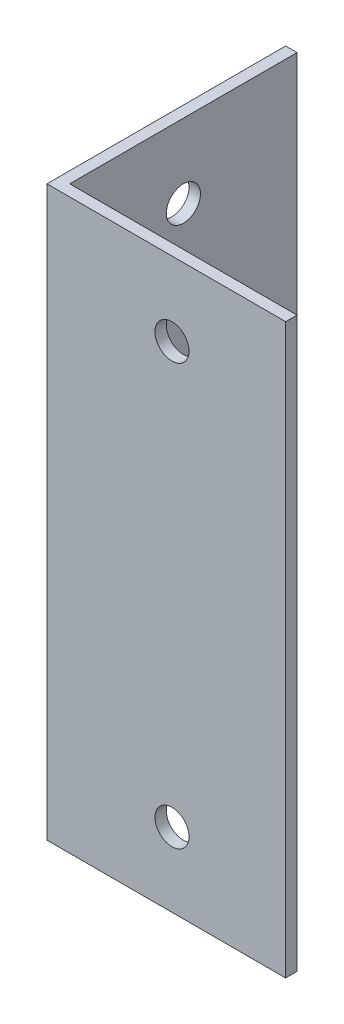
SolidWorks part; units mm, degrees
ref_plane "Face" through (0, 0, 0) normal (0, 0, 1) x (1, 0, 0)
ref_plane "Dessus" through (0, 0, 0) normal (0, 1, 0) x (1, 0, 0)
ref_plane "Droite" through (0, 0, 0) normal (1, 0, 0) x (0, 0, -1)
sketch "Esquisse1" plane through (0, 0, 0) normal (0, 1, 0) x (1, 0, 0)
  line L0 (0, 0) -> (0, 21)
  line L1 (0, 21) -> (1, 21)
  line L2 (1, 21) -> (1, 1)
  line L3 (1, 1) -> (21, 1)
  line L4 (21, 1) -> (21, 0)
  line L5 (21, 0) -> (0, 0)
  dimension "D1" = 1
  dimension "D2" = 1
  dimension "D3" = 90
  dimension "D4" = 20
extrude "Extrusion1" add sketch "Esquisse1" along normal blind 50
sketch "Esquisse2" plane through (1, 0, 0) normal (1, 0, 0) x (0, 0, -1)
  line L0 (1, 25) -> (21, 25) construction
  line L1 (1, 50) -> (1, 0) construction
  line L2 (21, 50) -> (21, 0) construction
  line L3 (11, 0) -> (11, 50) construction
  line L4 (1, 0) -> (21, 0) construction
  line L5 (1, 50) -> (21, 50) construction
  circle A0 centre (11, 6.5) radius 1.5
  circle A2 centre (11, 43.5) radius 1.5
  dimension "D1" = 3
  dimension "D2" = 18.5
extrude "Extrusion2" cut sketch "Esquisse2" against normal up to next
sketch "Esquisse3" plane through (0, 0, -1) normal (0, 0, -1) x (-1, 0, 0)
  line L0 (-11, 50) -> (-11, 0) construction
  line L1 (-21, 50) -> (-1, 50) construction
  line L2 (-21, 0) -> (-1, 0) construction
  line L3 (-21, 25) -> (-1, 25) construction
  line L4 (-21, 50) -> (-21, 0) construction
  line L5 (-1, 50) -> (-1, 0) construction
  circle A0 centre (-11, 43.5) radius 1.5
  circle A3 centre (-11, 6.5) radius 1.5
  dimension "D1" = 3
  dimension "D2" = 18.5
extrude "Extrusion3" cut sketch "Esquisse3" against normal up to next
